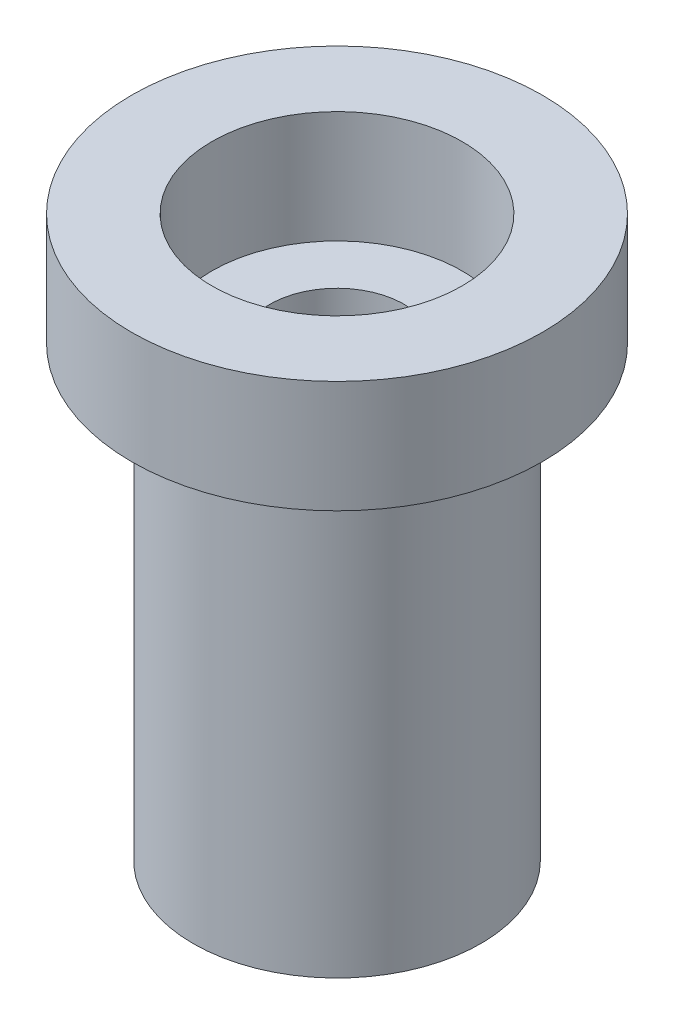
SolidWorks part; units mm, degrees
ref_plane "Front Plane" through (0, 0, 0) normal (0, 0, 1) x (1, 0, 0)
ref_plane "Top Plane" through (0, 0, 0) normal (0, 1, 0) x (1, 0, 0)
ref_plane "Right Plane" through (0, 0, 0) normal (1, 0, 0) x (0, 0, -1)
sketch "Sketch1" plane through (0, 0, 0) normal (0, 1, 0) x (1, 0, 0)
  circle A0 centre (0, 0) radius 3.85
  circle A1 centre (0, 0) radius 1.8
  dimension "D1" = 7.7
  dimension "D2" = 3.6
extrude "Boss-Extrude1" add sketch "Sketch1" along normal up to surface (12 mm away)
sketch "Sketch2" plane through (0, 12, 0) normal (0, 1, 0) x (1, 0, 0)
  line L0 (-0.3736, 2.8758) -> (1.2239, -9.4208) construction
  circle A0 centre (0, 0) radius 5.5
  circle A1 centre (0, 0) radius 3.35
  dimension "D1" = 6.7
  dimension "D2" = 11
extrude "Boss-Extrude2" add sketch "Sketch2" along normal blind 3
